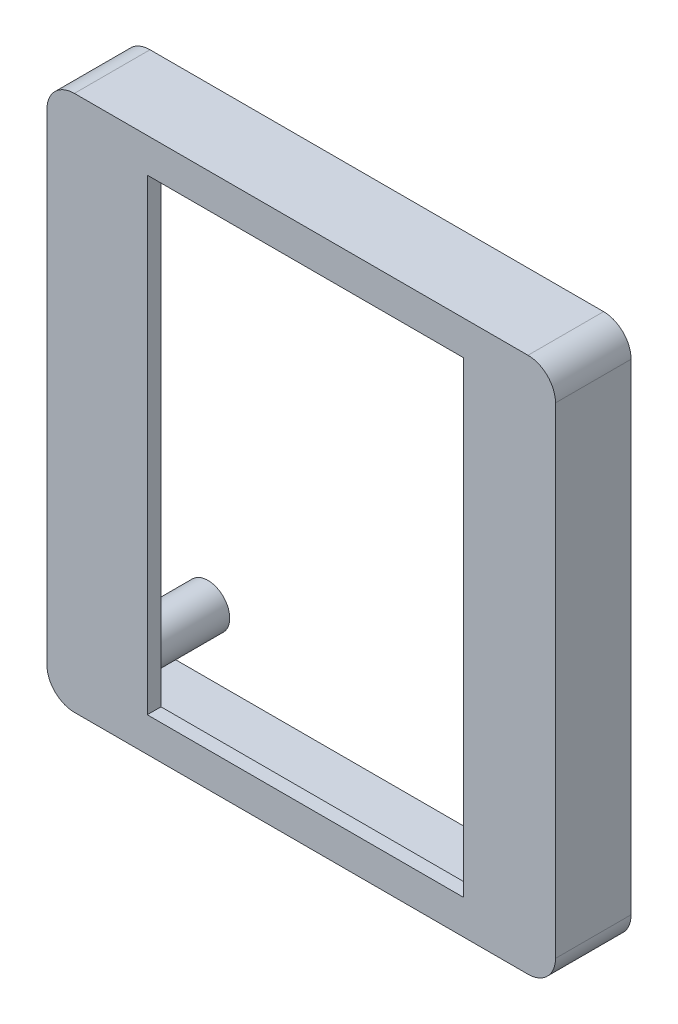
SolidWorks part; units mm, degrees
ref_plane "Alzado" through (0, 0, 0) normal (0, 0, 1) x (1, 0, 0)
ref_plane "Planta" through (0, 0, 0) normal (0, 1, 0) x (1, 0, 0)
ref_plane "Vista lateral" through (0, 0, 0) normal (1, 0, 0) x (0, 0, -1)
sketch "Croquis1" plane through (0, 0, 0) normal (0, 0, 1) x (1, 0, 0)
  circle A0 centre (14.7905, 1.2625) radius 1.5875
  circle A1 centre (14.7905, -29.5625) radius 1.5875
  circle A2 centre (-13.7845, -29.5625) radius 1.5875
  circle A3 centre (-13.7845, 1.2625) radius 1.5875
extrude "Saliente-Extruir1" add sketch "Croquis1" along normal up to surface (6.5 mm away)
sketch "Croquis2" plane through (0, 0, 2) normal (0, 0, 1) x (1, 0, 0)
  line L0 (-17.997, 3.35) -> (-17.997, -31.65)
  line L1 (-16.497, 3.85) -> (17.503, 3.85)
  line L2 (-16.497, 3.85) -> (-16.497, -32.15)
  line L3 (-16.497, -32.15) -> (17.503, -32.15)
  line L4 (17.503, 3.85) -> (17.503, -32.15)
  line L5 (-15.997, -33.65) -> (17.003, -33.65)
  line L6 (19.003, 3.35) -> (19.003, -31.65)
  line L7 (-15.997, 5.35) -> (17.003, 5.35)
  line L8 (-17.997, -33.65) -> (19.003, -33.65) construction
  line L9 (-17.997, 5.35) -> (-17.997, -33.65) construction
  line L10 (19.003, 5.35) -> (19.003, -33.65) construction
  line L11 (-17.997, 5.35) -> (19.003, 5.35) construction
  arc A0 (-15.997, -33.65) -> (-17.997, -31.65) centre (-15.997, -31.65) cw
  arc A1 (17.003, -33.65) -> (19.003, -31.65) centre (17.003, -31.65) ccw
  arc A2 (19.003, 3.35) -> (17.003, 5.35) centre (17.003, 3.35) ccw
  arc A3 (-15.997, 5.35) -> (-17.997, 3.35) centre (-15.997, 3.35) ccw
  arc M25 (-16.8212, -9.84) -> (-13.6728, -9.84) centre (-15.247, -9.84) cw
  arc M27 (-13.6728, -18.46) -> (-16.8212, -18.46) centre (-15.247, -18.46) cw
  line M28 (-16.8212, -18.46) -> (-16.8212, -9.84)
  dimension "D2" = 2
  dimension "D1" = 1.5
extrude "Saliente-Extruir2" add sketch "Croquis2" along normal up to surface (4.5 mm away) separate body contours L7 A3 L0 A0 L5 A1 L6 A2 L1 L4 L3 L2 M27 M28 M25
sketch "Croquis3" plane through (0, 0, 6.5) normal (0, 0, 1) x (1, 0, 0)
  line L1 (-10.697, 2.85) -> (12.303, 2.85)
  line L2 (-10.697, 2.85) -> (-10.697, -31.15)
  line L3 (-10.697, -31.15) -> (12.303, -31.15)
  line L4 (12.303, 2.85) -> (12.303, -31.15)
  line L12 (17.003, 5.35) -> (-15.997, 5.35)
  line L13 (-17.997, 3.35) -> (-17.997, -31.65)
  line L14 (-15.997, -33.65) -> (17.003, -33.65)
  line L15 (19.003, -31.65) -> (19.003, 3.35)
  line L16 (17.003, 5.35) -> (-15.997, 5.35)
  line L17 (-17.997, 3.35) -> (-17.997, -31.65)
  line L18 (-15.997, -33.65) -> (17.003, -33.65)
  line L19 (19.003, -31.65) -> (19.003, 3.35)
  arc A8 (-15.997, 5.35) -> (-17.997, 3.35) centre (-15.997, 3.35) ccw
  arc A9 (-17.997, -31.65) -> (-15.997, -33.65) centre (-15.997, -31.65) ccw
  arc A10 (17.003, -33.65) -> (19.003, -31.65) centre (17.003, -31.65) ccw
  arc A11 (19.003, 3.35) -> (17.003, 5.35) centre (17.003, 3.35) ccw
  arc A12 (-15.997, 5.35) -> (-17.997, 3.35) centre (-15.997, 3.35) ccw
  arc A13 (-17.997, -31.65) -> (-15.997, -33.65) centre (-15.997, -31.65) ccw
  arc A14 (17.003, -33.65) -> (19.003, -31.65) centre (17.003, -31.65) ccw
  arc A15 (19.003, 3.35) -> (17.003, 5.35) centre (17.003, 3.35) ccw
  line M13 (17.003, 5.35) -> (-15.997, 5.35)
  arc M14 (-15.997, 5.35) -> (-17.997, 3.35) centre (-15.997, 3.35) ccw
  line M15 (-17.997, 3.35) -> (-17.997, -31.65)
  arc M16 (-17.997, -31.65) -> (-15.997, -33.65) centre (-15.997, -31.65) ccw
  line M17 (-15.997, -33.65) -> (17.003, -33.65)
  arc M18 (17.003, -33.65) -> (19.003, -31.65) centre (17.003, -31.65) ccw
  line M19 (19.003, -31.65) -> (19.003, 3.35)
  arc M20 (19.003, 3.35) -> (17.003, 5.35) centre (17.003, 3.35) ccw
  line M21 (-16.497, -8.8831) -> (-16.497, 3.85)
  line M22 (-16.497, 3.85) -> (17.503, 3.85)
  line M23 (17.503, 3.85) -> (17.503, -32.15)
  line M24 (17.503, -32.15) -> (-16.497, -32.15)
  line M25 (-16.497, -32.15) -> (-16.497, -19.4169)
  arc M26 (-16.497, -19.4169) -> (-16.8212, -18.46) centre (-15.247, -18.46) cw
  line M27 (-16.8212, -18.46) -> (-16.8212, -9.84)
  arc M28 (-16.8212, -9.84) -> (-16.497, -8.8831) centre (-15.247, -9.84) cw
  dimension "D1" = 0
extrude "Saliente-Extruir3" add sketch "Croquis3" along normal blind 1 contours L1 L4 L3 L2 M21 M28 M27 M26 M25 M24 M23 M22 | M20 M13 M14 M15 M16 M17 M18 M19 M28 M21 M22 M23 M24 M25 M26 M27
